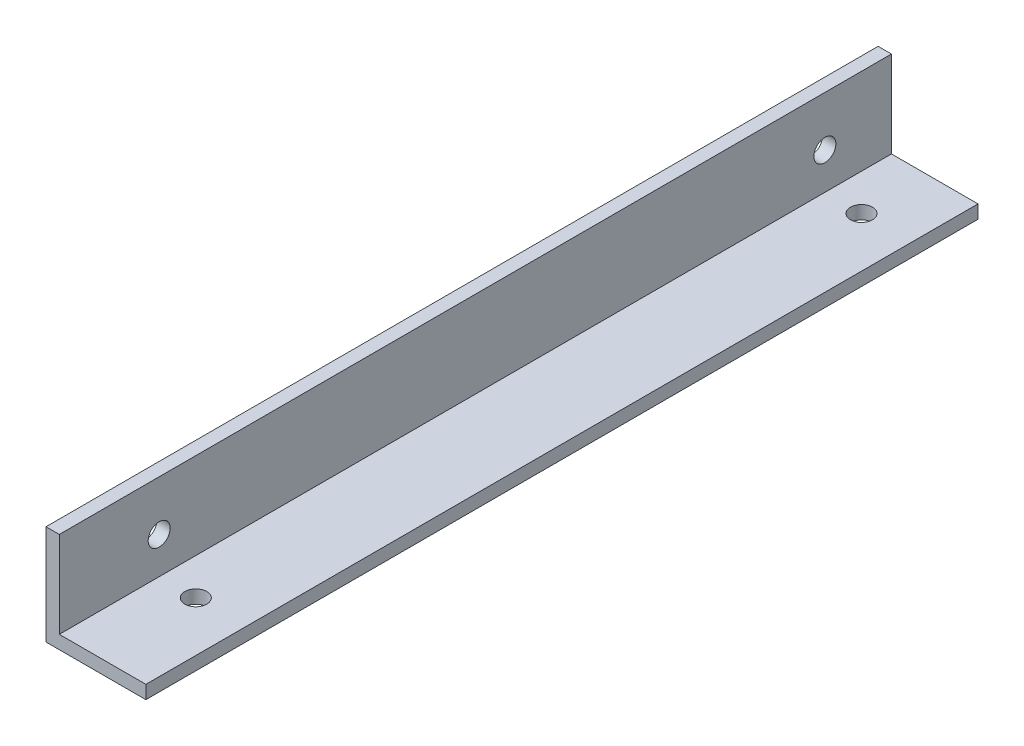
SolidWorks part; units mm, degrees
ref_plane "正面" through (0, 0, 0) normal (0, 0, 1) x (1, 0, 0)
ref_plane "平面" through (0, 0, 0) normal (0, 1, 0) x (1, 0, 0)
ref_plane "右側面" through (0, 0, 0) normal (1, 0, 0) x (0, 0, -1)
sketch "ｽｹｯﾁ1" plane through (0, 0, 0) normal (0, 0, 1) x (1, 0, 0)
  line L0 (0, 0) -> (15, 0)
  line L1 (15, 0) -> (15, 2)
  line L2 (15, 2) -> (2, 2)
  line L3 (2, 2) -> (2, 15)
  line L4 (2, 15) -> (0, 15)
  line L5 (0, 15) -> (0, 0)
  dimension "D1" = 15
  dimension "D2" = 15
  dimension "D3" = 2
  dimension "D4" = 2
extrude "ﾎﾞｽ - 押し出し1" add sketch "ｽｹｯﾁ1" along normal blind 125
sketch "ｽｹｯﾁ2" plane through (0, 0, 0) normal (-1, 0, 0) x (0, 0, 1)
  line L0 (0, 7.5) -> (10, 7.5)
  line L1 (0, 15) -> (0, 0) construction
  line L2 (10, 7.5) -> (110, 7.5)
  circle A0 centre (10, 7.5) radius 2.2
  circle A1 centre (110, 7.5) radius 2.2
  dimension "D3" = 4.4
  dimension "D4" = 4.4
  dimension "D1" = 10
  dimension "D2" = 100
sketch "ｽｹｯﾁ3" plane through (0, 0, 0) normal (0, -1, 0) x (-1, 0, 0)
  line L0 (-7.5, 0) -> (-7.5, -10)
  line L1 (0, 0) -> (-15, 0) construction
  line L2 (-7.5, -10) -> (-7.5, -110)
  circle A0 centre (-7.5, -10) radius 2.2
  circle A1 centre (-7.5, -110) radius 2.2
  dimension "D3" = 4.4
  dimension "D4" = 4.4
  dimension "D1" = 10
  dimension "D2" = 100
hole_wizard "M4x0.7 ねじ穴1" positions "3Dｽｹｯﾁ2" profile "ｽｹｯﾁ5" tap size "M4x0.7" standard "JIS"
sketch3d "3Dｽｹｯﾁ2"
  point P0 (7.5, 0, 10)
  point P3 (7.5, 0, 110)
  point P6 (0, 7.5, 110)
  point P9 (0, 7.5, 10)
sketch "ｽｹｯﾁ5" plane through (7.5, 0, 10) normal (1, 0, 0) x (0, 0, -1)
  line L0 (0, 0) -> (0, 12.4914)
  line L1 (0, 12.4914) -> (1.65, 11.5)
  line L2 (1.65, 11.5) -> (1.65, 0)
  line L5 (1.65, 0) -> (0, 0)
  line L10 (0, 12.4914) -> (-1.65, 11.5) construction
  line L11 (0, -6.35) -> (0, 107.95) construction
  dimension "ねじ下穴ﾄﾞﾘﾙ直径" = 3.3
  dimension "ねじ下穴ﾄﾞﾘﾙの深さ" = 11.5
  dimension "ﾄﾞﾘﾙ角度" = 118
cosmetic thread "穴のねじ山1" parameters "D1"=2, "D2"=4
cosmetic thread "穴のねじ山2" parameters "D1"=2, "D2"=4
cosmetic thread "穴のねじ山3" parameters "D1"=2, "D2"=4
cosmetic thread "穴のねじ山4" parameters "D1"=2, "D2"=4
